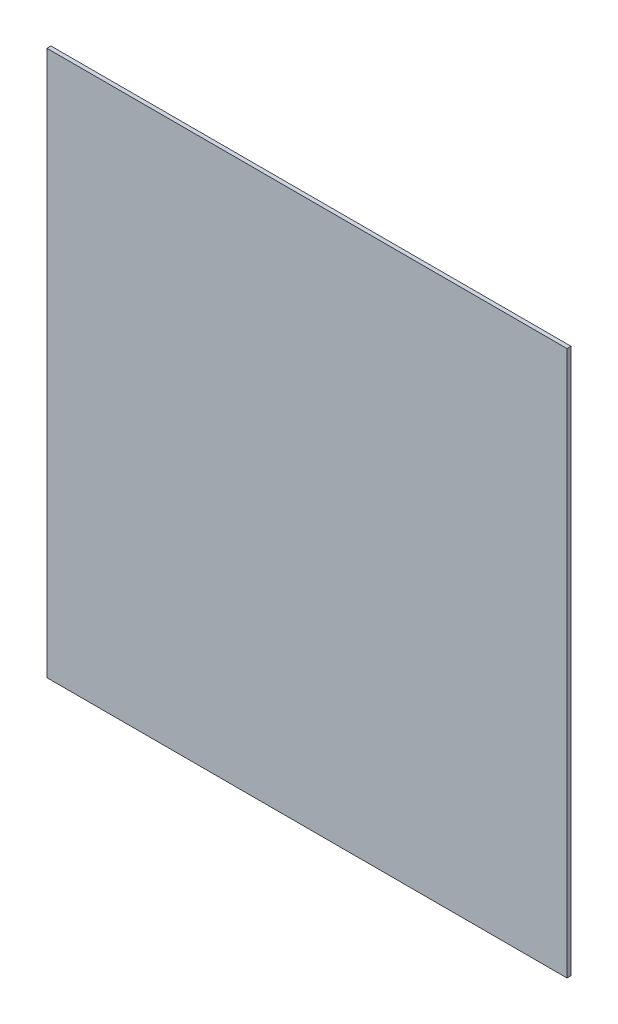
SolidWorks part; units mm, degrees
material "ABS PC"
ref_plane "Front Plane" through (0, 0, 0) normal (0, 0, 1) x (1, 0, 0)
ref_plane "Top Plane" through (0, 0, 0) normal (0, 1, 0) x (1, 0, 0)
ref_plane "Right Plane" through (0, 0, 0) normal (1, 0, 0) x (0, 0, -1)
sketch "Sketch1" plane through (0, 0, 0) normal (0, 0, 1) x (1, 0, 0)
  line L0 (-65.4525, -71.5962) -> (-65.4525, -97.0282) construction
  line L1 (-65.4525, -92.9166) -> (-81.8675, -92.9166)
  line L2 (-65.4525, -92.9166) -> (-65.4525, -75.7079)
  line L3 (-65.4525, -75.7079) -> (-81.8675, -75.7079)
  line L4 (-81.8675, -92.9166) -> (-81.8675, -75.7079)
  line L5 (-65.4525, -92.9166) -> (-81.8675, -75.7079) construction
  line L6 (-65.4525, -75.7079) -> (-81.8675, -92.9166) construction
  line L7 (-81.8675, -97.0282) -> (-81.8675, -71.5962) construction
  line L8 (-79.2162, -84.3122) -> (-68.1037, -84.3122) construction
  line L9 (-79.2162, -89.7574) -> (-79.2162, -78.8671) construction
  line L10 (-68.1037, -78.8671) -> (-68.1037, -89.7574) construction
  line L11 (-79.2162, -84.3122) -> (-81.8675, -84.3122) construction
  line L12 (-73.66, -92.9166) -> (-73.66, -90.2654) construction
  line L13 (-68.6117, -90.2654) -> (-78.7082, -90.2654) construction
  point P4 (-73.66, -84.3122)
extrude "Boss-Extrude1" add sketch "Sketch1" along normal blind 0.127
